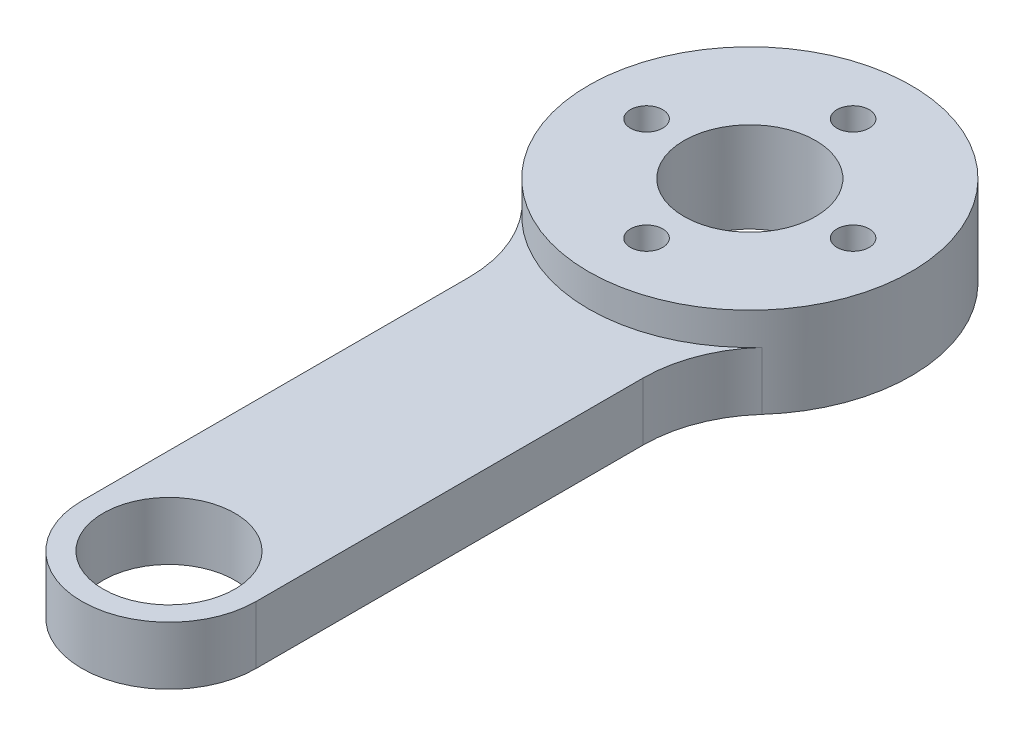
SolidWorks part; units mm, degrees
ref_plane "Front Plane" through (0, 0, 0) normal (0, 0, 1) x (1, 0, 0)
ref_plane "Top Plane" through (0, 0, 0) normal (0, 1, 0) x (1, 0, 0)
ref_plane "Right Plane" through (0, 0, 0) normal (1, 0, 0) x (0, 0, -1)
other "Center of Mass"
sketch "Sketch2" plane through (0, 0, 0) normal (0, 1, 0) x (1, 0, 0)
  line L0 (0, 0) -> (0, -34.6275) construction
  line L1 (-6.75, -10.5208) -> (-6.75, -45)
  line L2 (6.75, -10.5208) -> (6.75, -45)
  line L3 (0, 0) -> (0, 16.7999) construction
  circle A0 centre (0, 0) radius 12.5
  circle A1 centre (0, -45) radius 6.75
  circle A3 centre (0, -45) radius 5.1
  circle A4 centre (0, 8) radius 1.25
  circle A5 centre (8, 0) radius 1.25
  circle A6 centre (0, -8) radius 1.25
  circle A7 centre (-8, 0) radius 1.25
  point P24 (0, 0)
  dimension "D2" = 25
  dimension "D3" = 13.5
  dimension "D5" = 10.2
  dimension "D7" = 2.5
  dimension "D1" = 45
  dimension "D6" = 8
  dimension "D8" = 4
extrude "Boss-Extrude2" add sketch "Sketch2" along normal blind 4.5
fillet "Fillet1" radius 10 2 edges at (-6.75, 2.25, 10.5208) (6.75, 2.25, 10.5208)
sketch "Sketch4" plane through (0, 0, 0) normal (0, -1, 0) x (1, 0, 0)
  circle A0 centre (0, 8) radius 2
  circle A1 centre (-8, 0) radius 2
  circle A2 centre (8, 0) radius 2
  circle A3 centre (0, -8) radius 2
  circle A4 centre (0, 8) radius 1.25 construction
  circle A5 centre (-8, 0) radius 1.25 construction
  circle A6 centre (8, 0) radius 1.25 construction
  circle A7 centre (0, -8) radius 1.25 construction
  dimension "D1" = 4
extrude "Cut-Extrude1" cut sketch "Sketch4" against normal blind 2
sketch "Sketch5" plane through (0, 4.5, 0) normal (0, 1, 0) x (1, 0, 0)
  circle A0 centre (0, 0) radius 12.5
  circle A1 centre (8, 0) radius 1.25 construction
  circle A2 centre (0, 8) radius 1.25 construction
  circle A3 centre (-8, 0) radius 1.25 construction
  circle A4 centre (0, -8) radius 1.25 construction
  circle A5 centre (8, 0) radius 1.25
  circle A6 centre (0, 8) radius 1.25
  circle A7 centre (-8, 0) radius 1.25
  circle A8 centre (0, -8) radius 1.25
  arc A9 (9.3056, -8.3461) -> (-9.3056, -8.3461) centre (0, 0) ccw construction
extrude "Boss-Extrude3" add sketch "Sketch5" along normal blind 2.5
sketch "Sketch6" plane through (0, 4.5, 0) normal (0, 1, 0) x (1, 0, 0)
  line L0 (0, 0) -> (15.8699, 27.4874)
  line L1 (0, 0) -> (0, -12.5)
  line L2 (0, -12.5) -> (-19.6039, -12.5)
  line L3 (0, -12.5) -> (0, -23.25)
  arc A0 (-9.3056, -8.3461) -> (9.3056, -8.3461) centre (0, 0) ccw construction
  circle A1 centre (0, 0) radius 23.25
  circle A3 centre (0, 0) radius 12.5
  circle A4 centre (0, 0) radius 12.5
  arc M4 (-9.3056, -8.3461) -> (-6.75, -15.0229) centre (-16.75, -15.0229) cw
  line M5 (-6.75, -15.0229) -> (-6.75, -45)
  dimension "D2" = 46.5
  dimension "D3" = 150
  dimension "D1" = 0
extrude "Boss-Extrude4" [suppressed] add sketch "Sketch6" against normal up to surface (4.5 mm away) contours L2 A1 M5 M4 | A4 L0 A1 L2 M4
sketch "Sketch7" plane through (0, 4.5, 0) normal (0, 1, 0) x (1, 0, 0)
  line L0 (0, 0) -> (0, -76.7095) construction
  line L1 (0, 0) -> (35.6996, 0) construction
  line L2 (0, -9) -> (35.6996, -9) construction
  line L3 (0, -9) -> (0, -85.7095) construction
  line L4 (0, -18) -> (35.6996, -18) construction
  line L5 (0, -18) -> (0, -94.7095) construction
  line L6 (0, -27) -> (35.6996, -27) construction
  line L7 (0, -27) -> (0, -103.7095) construction
  line L8 (0, -36) -> (35.6996, -36) construction
  line L9 (0, -36) -> (0, -112.7095) construction
  circle A3 centre (0, -15.4603) radius 2.5
  circle A4 centre (0, -24.4603) radius 2.5
  circle A5 centre (0, -33.4603) radius 2.5
  circle A6 centre (0, -42.4603) radius 2.5
  circle A7 centre (0, -51.4603) radius 2.5
  dimension "D1" = 5
  dimension "D2" = 5
extrude "Cut-Extrude4" [suppressed] cut sketch "Sketch7" against normal blind 10
sketch "Sketch8" plane through (0, 0, 0) normal (0, -1, 0) x (1, 0, 0)
  circle A0 centre (0, 0) radius 5.1
  dimension "D1" = 10.2
extrude "Cut-Extrude5" cut sketch "Sketch8" against normal blind 10
